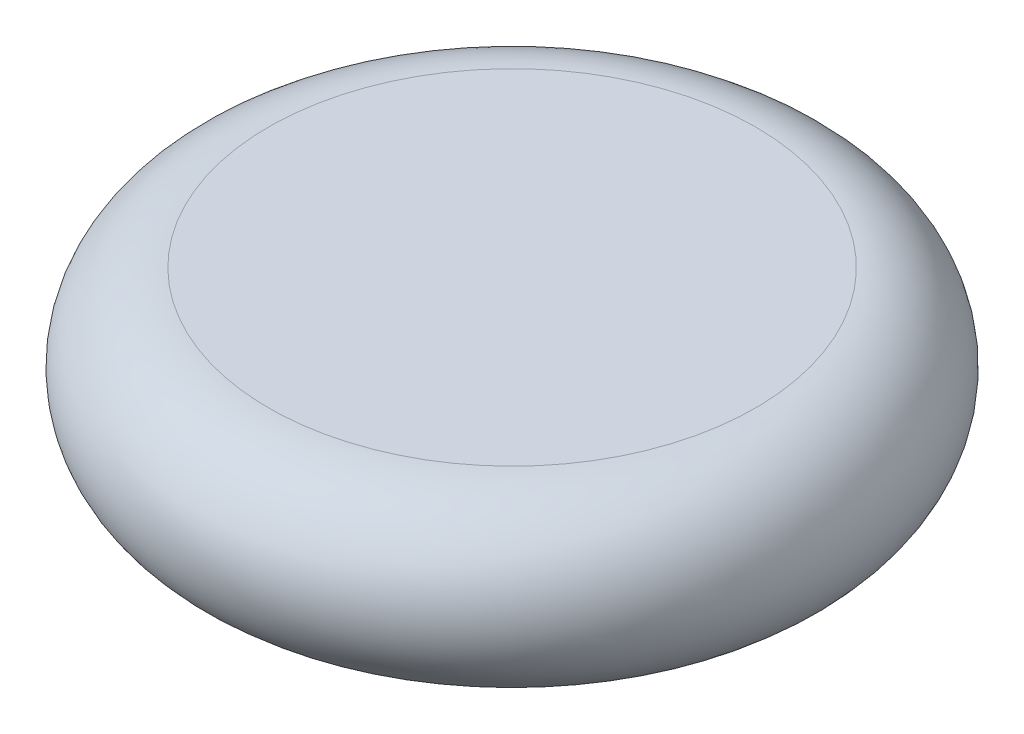
SolidWorks part; units mm, degrees
ref_plane "Front Plane" through (0, 0, 0) normal (0, 0, 1) x (1, 0, 0)
ref_plane "Top Plane" through (0, 0, 0) normal (0, 1, 0) x (1, 0, 0)
ref_plane "Right Plane" through (0, 0, 0) normal (1, 0, 0) x (0, 0, -1)
sketch "Sketch1" plane through (0, 0, 0) normal (1, 0, 0) x (0, 0, -1)
  line L1 (0, 0) -> (20.6322, 0)
  line L2 (0, 0) -> (0, 14.6156)
  line L3 (0, 14.6156) -> (20.6322, 14.6156)
  arc A0 (20.6322, 0) -> (20.6322, 14.6156) centre (20.6322, 7.3078) ccw
  point P6 (27.94, 7.3078)
  dimension "D1" = 14.6156
  dimension "D2" = 27.94
revolve "Revolve1" add sketch "Sketch1" angle 360 about L2
